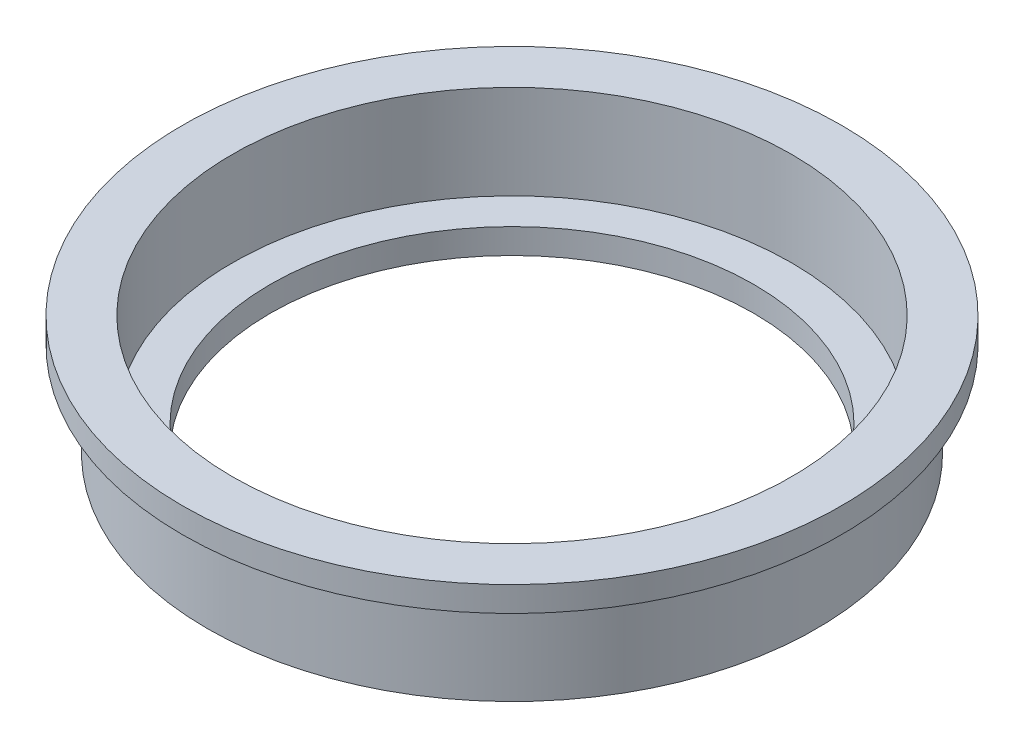
SolidWorks part; units mm, degrees
ref_plane "Front Plane" through (0, 0, 0) normal (0, 0, 1) x (1, 0, 0)
ref_plane "Top Plane" through (0, 0, 0) normal (0, 1, 0) x (1, 0, 0)
ref_plane "Right Plane" through (0, 0, 0) normal (1, 0, 0) x (0, 0, -1)
sketch "Sketch1" plane through (0, 0, 0) normal (0, 0, 1) x (1, 0, 0)
  line L0 (0, 0) -> (0, 14.2176) construction
  line L1 (24.511, 0) -> (24.511, 2.54)
  line L2 (24.511, 2.54) -> (28.321, 2.54)
  line L3 (28.321, 2.54) -> (28.321, 12.065)
  line L4 (28.321, 12.065) -> (33.401, 12.065)
  line L5 (33.401, 12.065) -> (33.401, 9.525)
  line L6 (33.401, 9.525) -> (30.861, 9.525)
  line L7 (30.861, 9.525) -> (30.861, 0)
  line L8 (30.861, 0) -> (24.511, 0)
  dimension "D1" = 9.525
  dimension "D2" = 3.81
  dimension "D3" = 5.08
  dimension "D4" = 2.54
  dimension "D5" = 2.54
  dimension "D6" = 56.642
  dimension "D7" = 2.54
revolve "Revolve1" add sketch "Sketch1" angle 360 about L0
equation "\"Aft closure lip axial\"= 0.375"
equation "\"aft closure lip holder\"= .15"
equation "\"Thrust plate connection\"= .2"
equation "\"D1@Sketch1\"=\"Aft closure lip axial\""
equation "\"D2@Sketch1\"=\"aft closure lip holder\""
equation "\"D3@Sketch1\"=\"Thrust plate connection\""
equation "\"retainer lip thickness\"= .1"
equation "\"D4@Sketch1\"=\"retainer lip thickness\""
equation "\"D5@Sketch1\"=\"retainer lip thickness\""
equation "\"Aft closure diameter\"= 2.230"
equation "\"D6@Sketch1\"=\"Aft closure diameter\""
